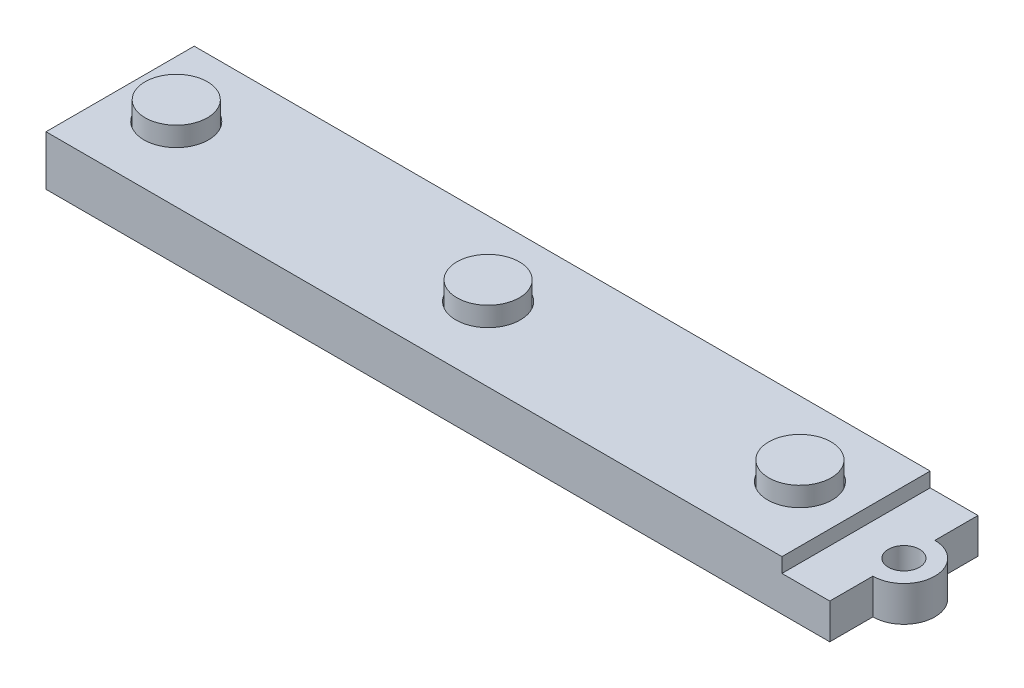
SolidWorks part; units mm, degrees
ref_plane "Front Plane" through (0, 0, 0) normal (0, 0, 1) x (1, 0, 0)
ref_plane "Top Plane" through (0, 0, 0) normal (0, 1, 0) x (1, 0, 0)
ref_plane "Right Plane" through (0, 0, 0) normal (1, 0, 0) x (0, 0, -1)
sketch "Sketch1" plane through (0, 0, 0) normal (0, 1, 0) x (1, 0, 0)
  line L1 (-116.1627, 34.9494) -> (-16.5947, 34.9494)
  line L2 (-116.1627, 34.9494) -> (-116.1627, 16.8392)
  line L3 (-116.1627, 16.8392) -> (-16.5947, 16.8392)
  line L4 (-16.5947, 34.9494) -> (-16.5947, 16.8392)
  dimension "D1" = 99.568
  dimension "D2" = 18.1102
extrude "Boss-Extrude1" add sketch "Sketch1" along normal blind 6.096
sketch "Sketch2" plane through (0, 6.096, 0) normal (0, 1, 0) x (1, 0, 0)
  line L0 (-16.5947, 34.9494) -> (-116.1627, 34.9494) construction
  line L1 (-26.2467, 34.9494) -> (-16.5947, 34.9494)
  line L2 (-26.2467, 34.9494) -> (-26.2467, 16.8392)
  line L3 (-26.2467, 16.8392) -> (-16.5947, 16.8392)
  line L4 (-16.5947, 34.9494) -> (-16.5947, 16.8392)
  line L5 (-116.1627, 34.9494) -> (-116.1627, 16.8392) construction
  dimension "D1" = 89.916
extrude "Cut-Extrude1" cut sketch "Sketch2" against normal blind 1.778
sketch "Sketch3" plane through (0, 4.318, 0) normal (0, 1, 0) x (1, 0, 0)
  line L0 (-20.4047, 34.9494) -> (-20.4047, 16.8392) construction
  line L1 (-16.5947, 34.9494) -> (-26.2467, 34.9494) construction
  line L2 (-26.2467, 16.8392) -> (-16.5947, 16.8392) construction
  line L3 (-16.5947, 16.8392) -> (-16.5947, 34.9494) construction
  circle A0 centre (-20.4047, 25.8943) radius 1.905
  dimension "D2" = 3.81
  dimension "D1" = 3.81
extrude "Cut-Extrude2" cut sketch "Sketch3" against normal through all
sketch "Sketch4" plane through (0, 6.096, 0) normal (0, 1, 0) x (1, 0, 0)
  line L0 (-26.2467, 34.9494) -> (-26.2467, 16.8392) construction
  circle A0 centre (-33.1047, 25.8943) radius 3.937
  circle A2 centre (-71.2047, 25.8943) radius 3.937
  circle A4 centre (-109.3047, 25.8943) radius 3.937
  circle A8 centre (-52.1547, 25.8943) radius 3.937 [skipped]
  circle A9 centre (-90.2547, 25.8943) radius 3.937 [skipped]
  dimension "D1" = 6.858
  dimension "D2" = 7.874
  dimension "D3" = 5
extrude "Cut-Extrude3" cut sketch "Sketch4" against normal blind 1.27
sketch "Sketch5" plane through (0, 0, 0) normal (0, -1, 0) x (1, 0, 0)
  line L0 (-26.2467, -34.9494) -> (-26.2467, -16.8392) construction
  line L1 (-16.5947, -34.9494) -> (-116.1627, -34.9494) construction
  line L2 (-116.1627, -16.8392) -> (-16.5947, -16.8392) construction
  line L3 (-116.1627, -34.9494) -> (-116.1627, -16.8392) construction
  line L4 (-116.1627, -34.9494) -> (-26.2467, -16.8392) construction
  line L6 (-29.9297, -32.2443) -> (-112.4797, -32.2443)
  line L7 (-29.9297, -32.2443) -> (-29.9297, -19.5443)
  line L8 (-29.9297, -19.5443) -> (-112.4797, -19.5443)
  line L9 (-112.4797, -32.2443) -> (-112.4797, -19.5443)
  line L10 (-29.9297, -32.2443) -> (-112.4797, -19.5443) construction
  line L11 (-29.9297, -19.5443) -> (-112.4797, -32.2443) construction
  point P9 (-71.2047, -25.8943)
  dimension "D1" = 89.916
  dimension "D2" = 12.7
  dimension "D3" = 82.55
extrude "Boss-Extrude2" add sketch "Sketch5" along normal blind 1.27
sketch "Sketch7" plane through (0, 4.318, 0) normal (0, 1, 0) x (1, 0, 0)
  line L0 (-20.4047, 34.9494) -> (-20.4047, 29.68) construction
  line L1 (-16.5947, 34.9494) -> (-26.2467, 34.9494) construction
  line L2 (-26.2467, 16.8392) -> (-16.5947, 16.8392) construction
  line L3 (-16.5947, 16.8392) -> (-16.5947, 34.9494) construction
  line L4 (-20.4047, 22.1085) -> (-20.4047, 16.8392) construction
  line L5 (-16.5947, 34.9494) -> (-20.4047, 34.9494)
  line L6 (-16.5947, 34.9494) -> (-16.5947, 16.8392)
  line L7 (-16.5947, 16.8392) -> (-20.4047, 16.8392)
  line L8 (-20.4047, 34.9494) -> (-20.4047, 29.68)
  line L9 (-20.4047, 22.1085) -> (-20.4047, 16.8392)
  arc A0 (-20.4047, 22.1085) -> (-20.4047, 29.68) centre (-20.4047, 25.8943) ccw
  dimension "D1" = 3.81
extrude "Cut-Extrude4" cut sketch "Sketch7" against normal through all
sketch "Sketch8" plane through (0, 4.826, 0) normal (0, 1, 0) x (1, 0, 0)
  circle A0 centre (-33.1047, 25.8943) radius 3.81
  circle A2 centre (-71.2047, 25.8943) radius 3.81
  circle A4 centre (-109.3047, 25.8943) radius 3.81
  circle A5 centre (-52.1547, 25.8943) radius 3.81 [skipped]
  circle A6 centre (-90.2547, 25.8943) radius 3.81 [skipped]
  dimension "D1" = 7.62
  dimension "D2" = 5
extrude "Boss-Extrude3" add sketch "Sketch8" along normal blind 3.556
